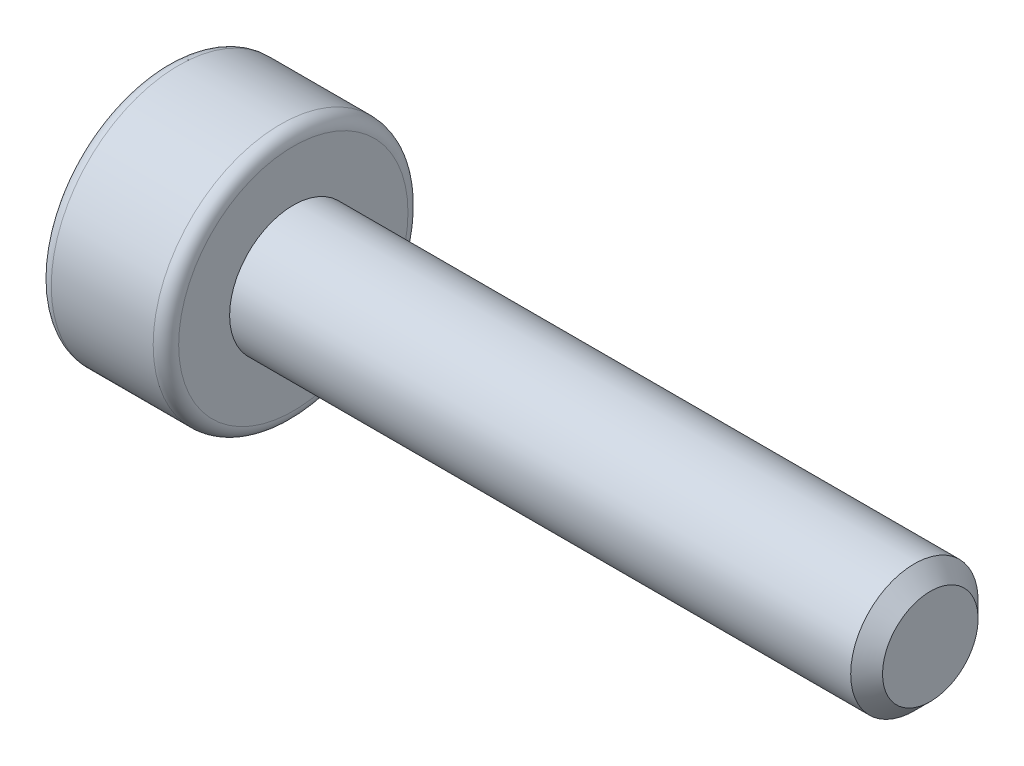
SolidWorks part; units mm, degrees
ref_plane "Front Plane" through (0, 0, 0) normal (0, 0, 1) x (1, 0, 0)
ref_plane "Top Plane" through (0, 0, 0) normal (0, 1, 0) x (1, 0, 0)
ref_plane "Right Plane" through (0, 0, 0) normal (1, 0, 0) x (0, 0, -1)
sketch "Sketch2" plane through (0, 0, 0) normal (0, 0, 1) x (1, 0, 0)
  line L0 (0, 0) -> (0, 1.8)
  line L1 (2, 1) -> (2, 1.8)
  line L2 (1.8, 2) -> (0.2, 2)
  line L3 (2, 1) -> (11.75, 1)
  line L4 (11.75, 1) -> (12, 0.75)
  line L5 (12, 0.75) -> (12, 0)
  line L6 (12, 0) -> (0, 0)
  line L7 (-2.2818, 0) -> (8.0811, 0) construction
  arc A0 (2, 1.8) -> (1.8, 2) centre (1.8, 1.8) ccw
  arc A1 (0, 1.8) -> (0.2, 2) centre (0.2, 1.8) cw
  point P13 (2, 2)
  point P16 (0, 2)
  dimension "D7" = 0.2
  dimension "D1" = 4
  dimension "D2" = 2
  dimension "D3" = 10
  dimension "D4" = 135
  dimension "D5" = 0.25
  dimension "D6" = 2
revolve "Revolve1" add sketch "Sketch2" angle 360 about L7
sketch "Sketch3" plane through (0, 0, 0) normal (-1, 0, 0) x (0, 0, 1)
  line L1 (0.433, -0.75) -> (0.866, 0)
  line L2 (0.866, 0) -> (0.433, 0.75)
  line L3 (0.433, 0.75) -> (-0.433, 0.75)
  line L4 (-0.433, 0.75) -> (-0.866, 0)
  line L5 (-0.866, 0) -> (-0.433, -0.75)
  line L6 (-0.433, -0.75) -> (0.433, -0.75)
  circle A0 centre (0, 0) radius 0.75 construction
  dimension "D1" = 1.5
extrude "Cut-Extrude1" cut sketch "Sketch3" against normal blind 0.8
